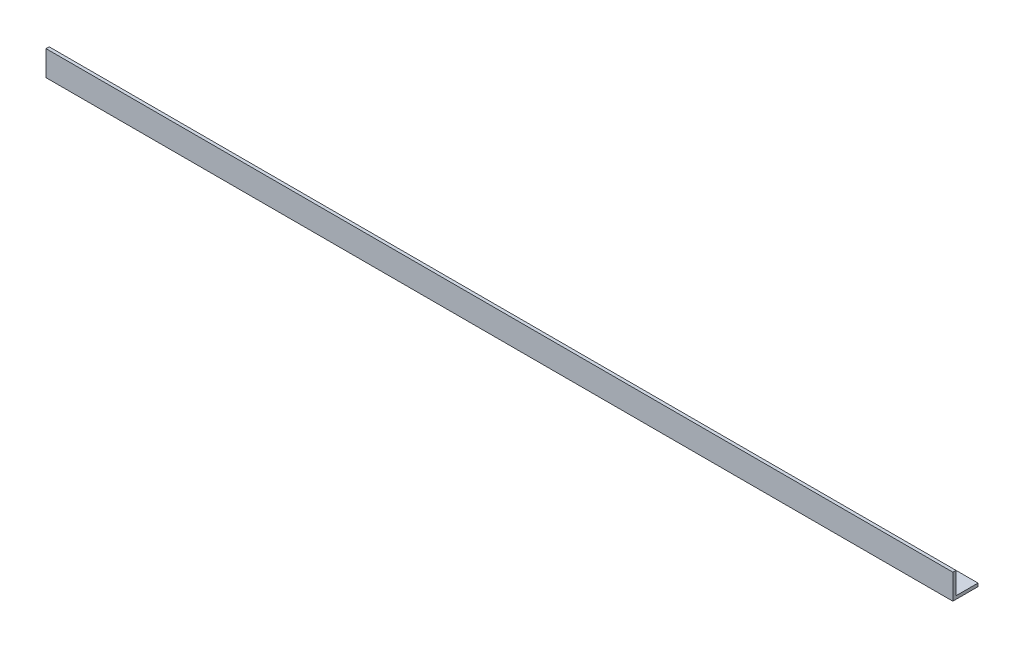
SolidWorks part; units mm, degrees
ref_plane "Front Plane" through (0, 0, 0) normal (0, 0, 1) x (1, 0, 0)
ref_plane "Top Plane" through (0, 0, 0) normal (0, 1, 0) x (1, 0, 0)
ref_plane "Right Plane" through (0, 0, 0) normal (1, 0, 0) x (0, 0, -1)
sketch "Sketch1" plane through (0, 0, 0) normal (1, 0, 0) x (0, 0, -1)
  line L0 (0, 0) -> (0, 25.4)
  line L1 (0, 25.4) -> (3.175, 25.4)
  line L2 (3.175, 25.4) -> (3.175, 3.175)
  line L3 (3.175, 3.175) -> (25.4, 3.175)
  line L4 (25.4, 3.175) -> (25.4, 0)
  line L5 (25.4, 0) -> (0, 0)
  dimension "D1" = 25.4
  dimension "D2" = 3.175
extrude "Boss-Extrude1" add sketch "Sketch1" along normal mid plane 914.4
